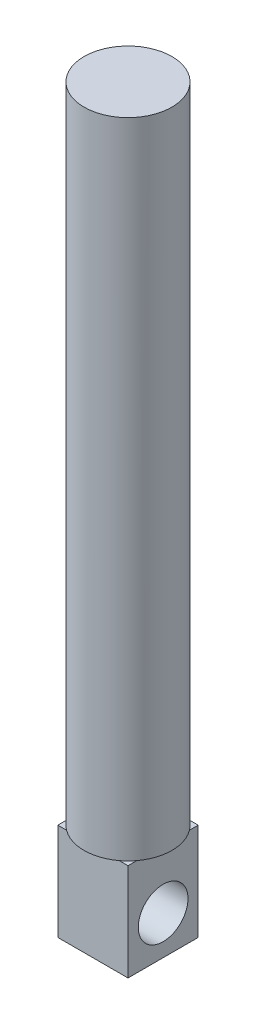
SolidWorks part; units mm, degrees
ref_plane "Front Plane" through (0, 0, 0) normal (0, 0, 1) x (1, 0, 0)
ref_plane "Top Plane" through (0, 0, 0) normal (0, 1, 0) x (1, 0, 0)
ref_plane "Right Plane" through (0, 0, 0) normal (1, 0, 0) x (0, 0, -1)
sketch "Sketch1" plane through (0, 0, 0) normal (0, 1, 0) x (1, 0, 0)
  line L1 (0, 0) -> (6, 0)
  line L2 (0, 0) -> (0, 6)
  line L3 (0, 6) -> (6, 6)
  line L4 (6, 0) -> (6, 6)
  dimension "D1" = 6
  dimension "D2" = 6
extrude "Boss-Extrude1" add sketch "Sketch1" along normal blind 8.31
sketch "Sketch2" plane through (6, 0, 0) normal (1, 0, 0) x (0, 0, -1)
  line L0 (0, 8.31) -> (6, 8.31) construction
  circle A0 centre (3, 3.31) radius 2.125
  dimension "D1" = 5
extrude "Cut-Extrude1" cut sketch "Sketch2" against normal blind 10
sketch "Sketch3" plane through (0, 8.31, 0) normal (0, 1, 0) x (1, 0, 0)
  line L0 (3, 0) -> (3, 6) construction
  line L1 (0, 0) -> (6, 0) construction
  line L2 (6, 6) -> (0, 6) construction
  line L3 (0, 3) -> (6, 3) construction
  line L4 (0, 6) -> (0, 0) construction
  line L5 (6, 0) -> (6, 6) construction
  circle A0 centre (3, 3) radius 3.75
extrude "Boss-Extrude2" add sketch "Sketch3" along normal blind 55
